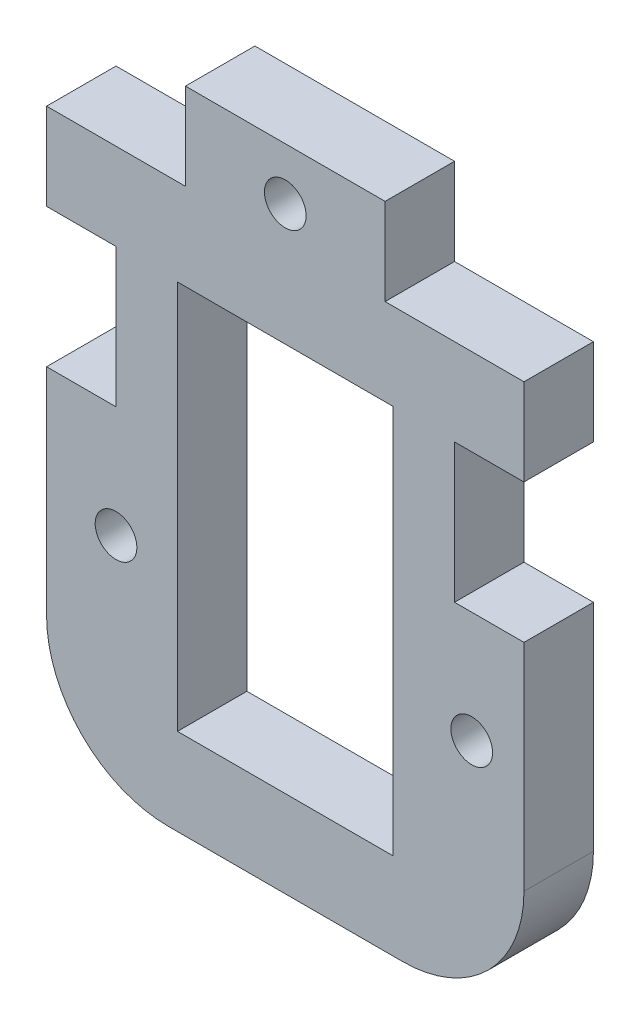
SolidWorks part; units mm, degrees
ref_plane "Front Plane" through (0, 0, 0) normal (0, 0, 1) x (1, 0, 0)
ref_plane "Top Plane" through (0, 0, 0) normal (0, 1, 0) x (1, 0, 0)
ref_plane "Right Plane" through (0, 0, 0) normal (1, 0, 0) x (0, 0, -1)
sketch "Sketch1" plane through (0, 0, 0) normal (0, 0, 1) x (1, 0, 0)
  line L0 (8, 32.42) -> (8, 37.42)
  line L1 (0, 0) -> (27.5, 0)
  line L2 (0, 0) -> (0, 32.42)
  line L4 (27.5, 0) -> (27.5, 32.42)
  line L7 (0, 32.42) -> (8, 32.42)
  line L11 (27.5, 32.42) -> (19.5, 32.42)
  line L14 (7.54, 27.42) -> (19.96, 27.42)
  line L15 (7.54, 27.42) -> (7.54, 5)
  line L16 (7.54, 5) -> (19.96, 5)
  line L17 (19.96, 27.42) -> (19.96, 5)
  line L18 (11.25, 27.42) -> (16.25, 27.42)
  line L19 (11.25, 27.42) -> (11.25, 28.42)
  line L20 (11.25, 28.42) -> (16.25, 28.42)
  line L21 (16.25, 27.42) -> (16.25, 28.42)
  line L22 (8, 37.42) -> (19.5, 37.42)
  line L23 (19.5, 37.42) -> (19.5, 32.42)
  line L24 (0, 27.42) -> (4, 27.42)
  line L25 (0, 27.42) -> (0, 19.42)
  line L26 (0, 19.42) -> (4, 19.42)
  line L27 (4, 27.42) -> (4, 19.42)
  line L28 (27.5, 27.42) -> (23.5, 27.42)
  line L29 (27.5, 27.42) -> (27.5, 19.42)
  line L30 (27.5, 19.42) -> (23.5, 19.42)
  line L31 (23.5, 27.42) -> (23.5, 19.42)
  circle A0 centre (24.49, 13.01) radius 1.2
  circle A1 centre (24.49, 13.01) radius 1.2 construction
  circle A2 centre (13.75, 21.21) radius 6.21
  arc A3 (10.9091, 15.6879) -> (16.5909, 15.6879) centre (13.75, 15.46) ccw
  circle A4 centre (4, 13) radius 1.2
  circle A5 centre (13.75, 34.42) radius 1.2
  point P9 (23.5, 32.42)
  point P15 (13.75, 37.42)
  point P21 (13.75, 27.42)
  point P22 (13.75, 5)
  point P27 (13.75, 28.42)
  point P28 (16.25, 27.92)
  point P34 (13.75, 0)
  dimension "D11" = 4
  dimension "D14" = 2.85
  dimension "D15" = 2.4
  dimension "D12" = 4
  dimension "D2" = 11.5
  dimension "D3" = 8
  dimension "D4" = 22.42
  dimension "D5" = 12.42
  dimension "D6" = 27.5
  dimension "D7" = 13
  dimension "D8" = 5
  dimension "D9" = 1
  dimension "D10" = 5
  dimension "D13" = 5.75
  dimension "D16" = 5
  dimension "D17" = 7
  dimension "D18" = 5
  dimension "D19" = 5
  dimension "D20" = 8
extrude "Boss-Extrude1" add sketch "Sketch1" along normal blind 4
fillet "Fillet1" radius 7 2 edges at (0, 0, 2) (27.5, 0, 2)
